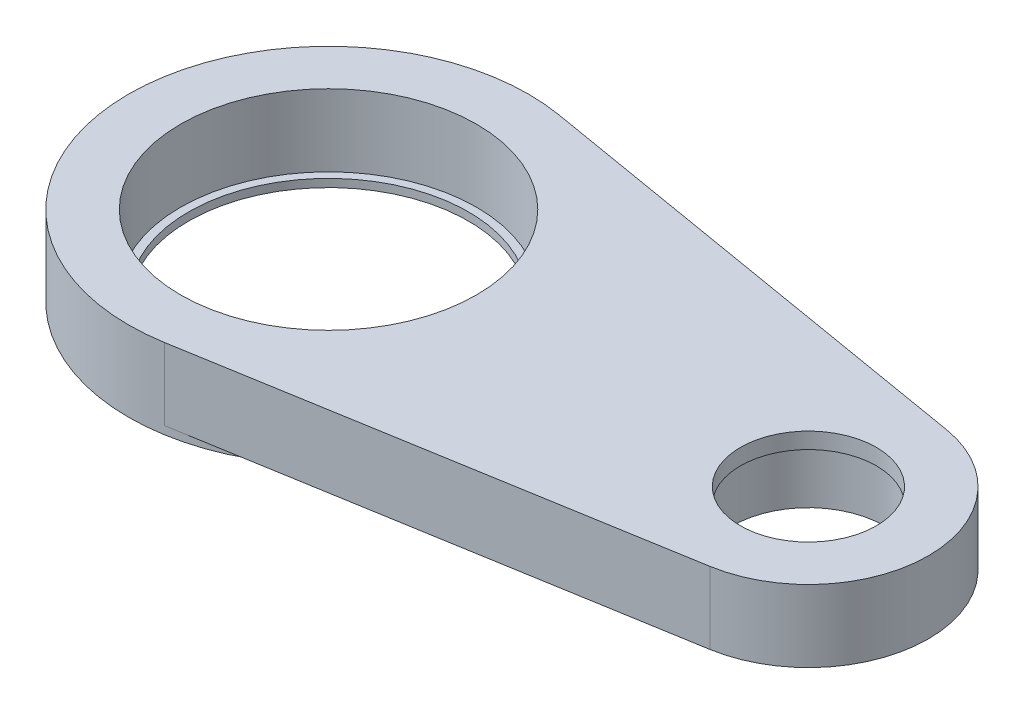
SolidWorks part; units mm, degrees
other "마크업1"
sketch "스케치8" plane through (80, 10, 22.5) normal (0.0741, 0.9433, 0.3234) x (0.9972, -0.0727, -0.0163)
sketch "스케치15" plane through (100, 13, 22.5) normal (0.0741, 0.9433, 0.3234) x (0.9972, -0.0727, -0.0163)
sketch "스케치16" plane through (100, 13, 22.5) normal (0.0741, 0.9433, 0.3234) x (0.9972, -0.0727, -0.0163)
sketch "스케치17" plane through (75, 13, 22.5) normal (0.0741, 0.9433, 0.3234) x (0.9972, -0.0727, -0.0163)
sketch "스케치23" plane through (75, 13, 22.5) normal (0.0741, 0.9433, 0.3234) x (0.9972, -0.0727, -0.0163)
sketch "스케치24" plane through (75, 10, 22.5) normal (0.0741, 0.9433, 0.3234) x (0.9972, -0.0727, -0.0163)
material "7075-T6 (SN)"
ref_plane "정면" through (0, 0, 0) normal (0, 0, 1) x (1, 0, 0)
ref_plane "윗면" through (0, 0, 0) normal (0, 1, 0) x (1, 0, 0)
ref_plane "우측면" through (0, 0, 0) normal (1, 0, 0) x (0, 0, -1)
sketch "스케치1" plane through (0, 0, 0) normal (0, 1, 0) x (1, 0, 0)
  circle A0 centre (0, 0) radius 17.5
  circle A1 centre (0, 0) radius 25
  dimension "D1" = 35
  dimension "D2" = 50
extrude "보스-돌출1" add sketch "스케치1" along normal blind 5 contours A1 | A0
sketch "스케치2" plane through (0, 5, 0) normal (0, 1, 0) x (1, 0, 0)
  circle A0 centre (0, 0) radius 18.5
  circle A1 centre (0, 0) radius 25 construction
  circle A2 centre (0, 0) radius 25
  dimension "D1" = 37
extrude "보스-돌출2" add sketch "스케치2" along normal blind 5
sketch "스케치3" plane through (0, 10, 0) normal (0, 1, 0) x (1, 0, 0)
  line L0 (4.1667, 24.6503) -> (62.5, 14.7902)
  line L1 (0, 0) -> (60, 0) construction
  line L2 (4.1667, -24.6503) -> (62.5, -14.7902)
  circle A0 centre (0, 0) radius 25 construction
  arc A1 (4.1667, -24.6503) -> (4.1667, 24.6503) centre (0, 0) ccw
  arc A2 (62.5, -14.7902) -> (62.5, 14.7902) centre (60, 0) ccw
  dimension "D2" = 30
  dimension "D1" = 60
extrude "보스-돌출3" add sketch "스케치3" against normal blind 9
sketch "스케치7" plane through (0, 5, 0) normal (0, 1, 0) x (1, 0, 0)
  circle A0 centre (0, 0) radius 18.5 construction
  circle A1 centre (0, 0) radius 18.5
extrude "컷-돌출4" cut sketch "스케치7" against normal blind 4
sketch "스케치13" plane through (0, 1, 0) normal (0, -1, 0) x (1, 0, 0)
  circle A0 centre (60, 0) radius 9.5
  dimension "D1" = 19
extrude "컷-돌출9" cut sketch "스케치13" against normal blind 7
sketch "스케치14" plane through (0, 8, 0) normal (0, -1, 0) x (1, 0, 0)
  circle A0 centre (60, 0) radius 8.5
  dimension "D1" = 17
extrude "컷-돌출10" cut sketch "스케치14" against normal through all
